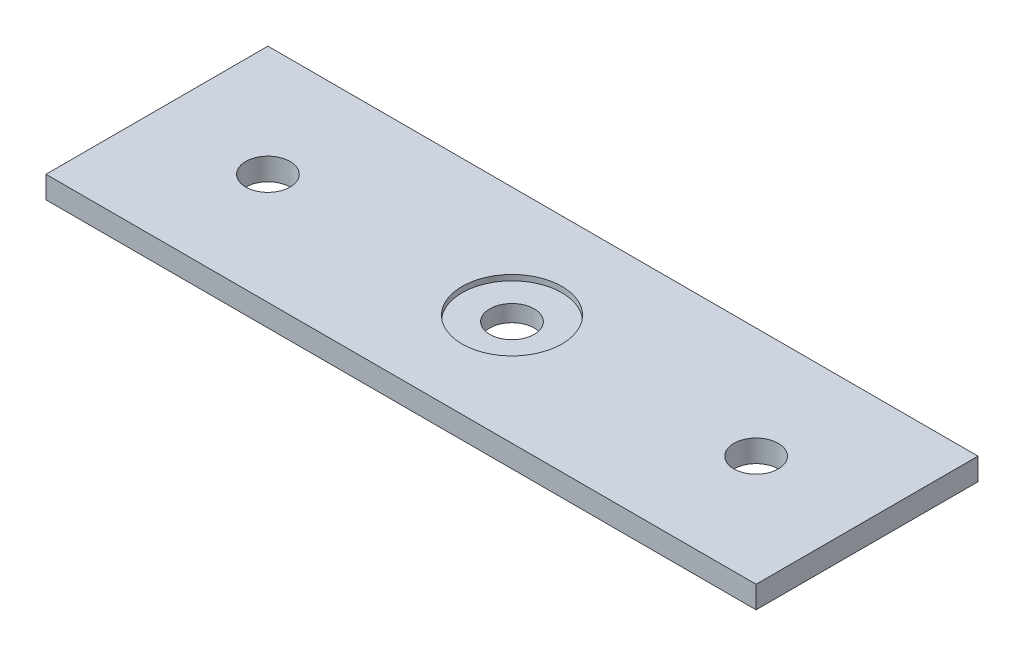
SolidWorks part; units mm, degrees
material "6061 Alloy"
ref_plane "Front" through (0, 0, 0) normal (0, 0, 1) x (1, 0, 0)
ref_plane "Top" through (0, 0, 0) normal (0, 1, 0) x (1, 0, 0)
ref_plane "Right" through (0, 0, 0) normal (1, 0, 0) x (0, 0, -1)
sketch "Sketch8" plane through (0, 0, 0) normal (0, 1, 0) x (1, 0, 0)
  line L0 (-101.6, 63.5) -> (-101.6, 0) construction
  line L1 (0, 0) -> (-203.2, 0)
  line L2 (0, 0) -> (0, 63.5)
  line L3 (0, 63.5) -> (-203.2, 63.5)
  line L4 (-203.2, 0) -> (-203.2, 63.5)
  dimension "D1" = 63.5
  dimension "D2" = 203.2
extrude "Boss-Extrude1" add sketch "Sketch8" along normal blind 6.35
sketch "Sketch9" plane through (0, 6.35, 0) normal (0, 1, 0) x (1, 0, 0)
  line L0 (-101.6, 63.5) -> (-101.6, 0) construction
  line L1 (0, 63.5) -> (-203.2, 63.5) construction
  line L2 (-203.2, 0) -> (0, 0) construction
  circle A0 centre (-101.6, 31.75) radius 14.2875
  dimension "D1" = 28.575
extrude "Cut-Extrude2" cut sketch "Sketch9" against normal blind 1.5875
sketch "Sketch10" plane through (0, 4.7625, 0) normal (0, 1, 0) x (1, 0, 0)
  circle A0 centre (-101.6, 31.75) radius 6.35
  dimension "D1" = 12.7
extrude "Cut-Extrude3" cut sketch "Sketch10" against normal through all
sketch "Sketch11" plane through (0, 6.35, 0) normal (0, 1, 0) x (1, 0, 0)
  line L0 (-203.2, 31.75) -> (0, 31.75) construction
  line L1 (-203.2, 63.5) -> (-203.2, 0) construction
  line L2 (0, 0) -> (0, 63.5) construction
  circle A0 centre (-171.45, 31.75) radius 6.35
  circle A1 centre (-31.75, 31.75) radius 6.35
  dimension "D1" = 12.7
  dimension "D3" = 12.7
  dimension "D2" = 31.75
  dimension "D4" = 31.75
extrude "Cut-Extrude4" cut sketch "Sketch11" against normal through all
